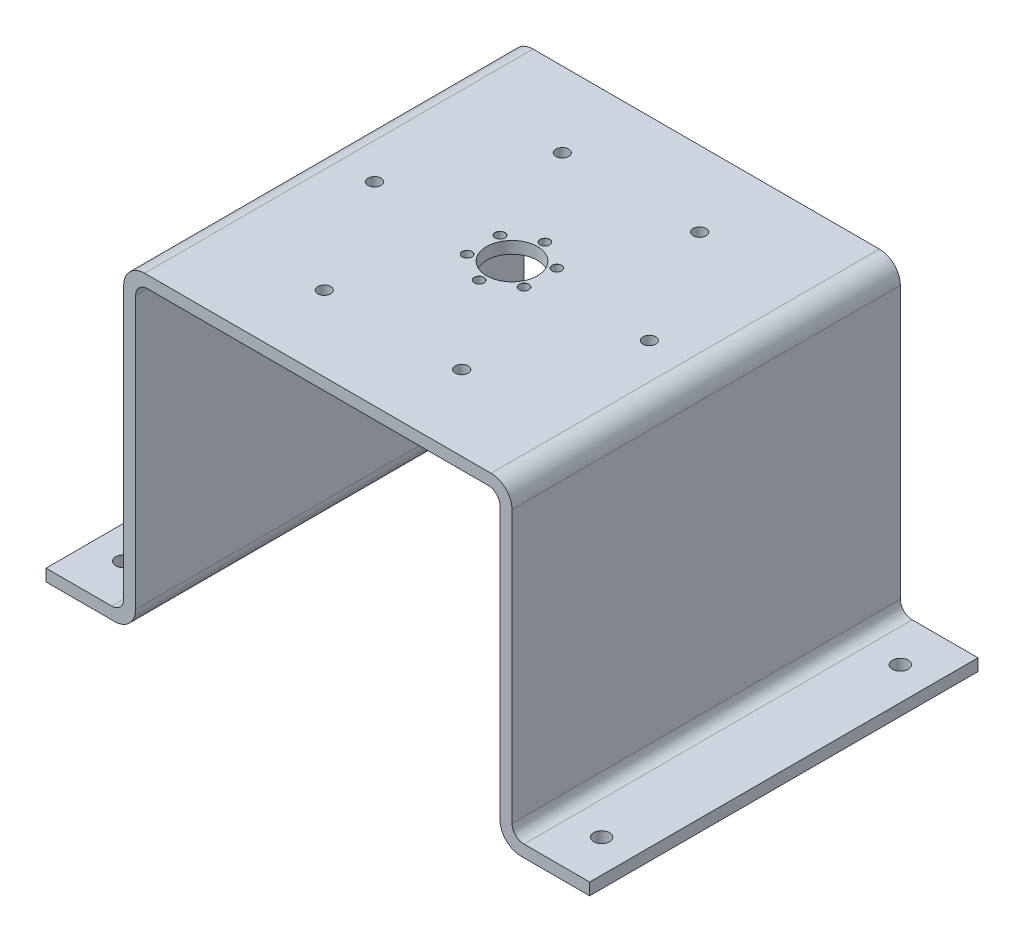
SolidWorks part; units mm, degrees
material "Plain Carbon Steel"
ref_plane "Front" through (0, 0, 0) normal (0, 0, 1) x (1, 0, 0)
ref_plane "Top" through (0, 0, 0) normal (0, 1, 0) x (1, 0, 0)
ref_plane "Right" through (0, 0, 0) normal (1, 0, 0) x (0, 0, -1)
sketch "Sketch1" plane through (0, 0, 0) normal (0, 0, 1) x (1, 0, 0)
  line L0 (0, 4) -> (26, 4)
  line L1 (0, 0) -> (30, 0)
  line L2 (30, 0) -> (30, 102)
  line L3 (30, 102) -> (152, 102)
  line L4 (152, 102) -> (152, 0)
  line L5 (152, 0) -> (182, 0)
  line L6 (26, 4) -> (26, 106)
  line L7 (26, 106) -> (156, 106)
  line L8 (156, 106) -> (156, 4)
  line L9 (156, 4) -> (182, 4)
  line L10 (0, 4) -> (0, 0)
  line L11 (182, 4) -> (182, 0)
  dimension "D1" = 30
  dimension "D2" = 102
  dimension "D3" = 4
  dimension "D4" = 30
  dimension "D5" = 130
extrude "Boss-Extrude1" add sketch "Sketch1" along normal blind 130
fillet "Fillet1" radius 4 4 edges at (152, 102, 65) (30, 102, 65) (26, 4, 65) (156, 4, 65)
fillet "Fillet2" radius 7 4 edges at (30, 0, 65) (152, 0, 65) (26, 106, 65) (156, 106, 65)
sketch "Sketch2" plane through (0, 106, 0) normal (0, 1, 0) x (1, 0, 0)
  line L0 (149, -130) -> (149, 0) construction
  line L2 (149, 0) -> (33, 0) construction
  circle A0 centre (91, -65) radius 8.5
  dimension "D1" = 17
  dimension "D3" = 65
  dimension "D2" = 58
extrude "Cut-Extrude1" cut sketch "Sketch2" against normal blind 100
hole_wizard "M3 Clearance Hole1" positions "Sketch4" profile "Sketch3" hole size "M3" standard "ISO" end condition through all
sketch "Sketch4" plane through (0, 106, 0) normal (0, 1, 0) x (1, 0, 0)
  line L2 (91, -65) -> (91, -54)
  circle A0 centre (91, -65) radius 8.5
  point P6 (91, -54)
  point P16 (100.5263, -59.5)
  point P17 (100.5263, -70.5)
  point P18 (91, -76)
  point P19 (81.4737, -70.5)
  point P20 (81.4737, -59.5)
  point P21 (91, -65)
  dimension "D1" = 11
  dimension "D3" = 0
  dimension "D2" = 6
sketch "Sketch3" plane through (91, 106, 54) normal (1, 0, 0) x (0, 0, 1)
  line L0 (0, 0) -> (0, 106)
  line L1 (0, 106) -> (1.6, 106)
  line L2 (1.6, 106) -> (1.6, 0.025)
  line L3 (1.6, 0.025) -> (1.625, 0)
  line L5 (1.625, 0) -> (0, 0)
  line L6 (-1.6, 0.025) -> (-1.625, 0) construction
  line L11 (0, -6.35) -> (0, 107.95) construction
  dimension "Thru Hole Dia." = 3.2
  dimension "Thru Hole Depth" = 106
  dimension "Near C'Sink Dia." = 3.25
  dimension "Near C'Sink Angle" = 90
sketch "Sketch12" plane through (0, 106, 0) normal (0, 1, 0) x (1, 0, 0)
  circle A0 centre (91, -65) radius 3.5935
hole_wizard "M4 Clearance Hole1" positions "Sketch7" profile "Sketch6" hole size "M4" standard "ISO"
sketch "Sketch7" plane through (0, 106, 0) normal (0, 1, 0) x (1, 0, 0)
  circle A0 centre (91, -65) radius 8.5 construction
  point P121 (137, -65)
  point P132 (114, -104.8372)
  point P133 (68, -104.8372)
  point P134 (45, -65)
  point P135 (68, -25.1628)
  point P136 (114, -25.1628)
  point P137 (91, -65)
  dimension "D1" = 46
  dimension "D3" = 0
  dimension "D5" = 0
  dimension "D4" = 0
  dimension "D2" = 6
sketch "Sketch6" plane through (137, 106, 65) normal (1, 0, 0) x (0, 0, 1)
  line L0 (0, 0) -> (0, 101.2919)
  line L1 (0, 101.2919) -> (2.15, 100)
  line L2 (2.15, 100) -> (2.15, 0)
  line L5 (2.15, 0) -> (0, 0)
  line L10 (0, 101.2919) -> (-2.15, 100) construction
  line L11 (0, -6.35) -> (0, 107.95) construction
  dimension "Hole Dia." = 4.3
  dimension "Hole Depth" = 100
  dimension "Drill Angle" = 118
sketch "Sketch5" plane through (0, 106, 0) normal (0, 1, 0) x (1, 0, 0)
  circle A0 centre (91, -65) radius 14.5
  dimension "D1" = 29
extrude "Cut-Extrude2" [suppressed] cut sketch "Sketch5" against normal blind 2
hole_wizard "M5 Clearance Hole2" positions "Sketch11" profile "Sketch10" hole size "M5" standard "ISO"
sketch "Sketch11" plane through (0, 4, 0) normal (0, 1, 0) x (1, 0, 0)
  line L0 (22, 0) -> (0, 0) construction
  line L1 (0, -130) -> (0, 0) construction
  line L2 (22, -130) -> (0, -130) construction
  line L3 (91, 0) -> (91, -10.4632)
  line L4 (149, 0) -> (33, 0) construction
  point P0 (11, -15)
  point P2 (11, -115)
  point P21 (171, -115)
  point P22 (171, -15)
  dimension "D1" = 15
  dimension "D2" = 11
  dimension "D3" = 11
  dimension "D4" = 15
sketch "Sketch10" plane through (11, 4, 15) normal (1, 0, 0) x (0, 0, 1)
  line L0 (0, 0) -> (0, 101.5923)
  line L1 (0, 101.5923) -> (2.65, 100)
  line L2 (2.65, 100) -> (2.65, 0)
  line L5 (2.65, 0) -> (0, 0)
  line L10 (0, 101.5923) -> (-2.65, 100) construction
  line L11 (0, -6.35) -> (0, 107.95) construction
  dimension "Hole Dia." = 5.3
  dimension "Hole Depth" = 100
  dimension "Drill Angle" = 118
sketch "Sketch13" plane through (0, 0, 130) normal (0, 0, 1) x (1, 0, 0)
  line L1 (0, 0) -> (25, 0)
  line L2 (0, 0) -> (0, 100.9002)
  line L3 (0, 100.9002) -> (25, 100.9002)
  line L4 (25, 0) -> (25, 100.9002)
  line L5 (182, 0) -> (117, 0)
  line L6 (182, 0) -> (182, 102.4575)
  line L7 (182, 102.4575) -> (117, 102.4575)
  line L8 (117, 0) -> (117, 102.4575)
